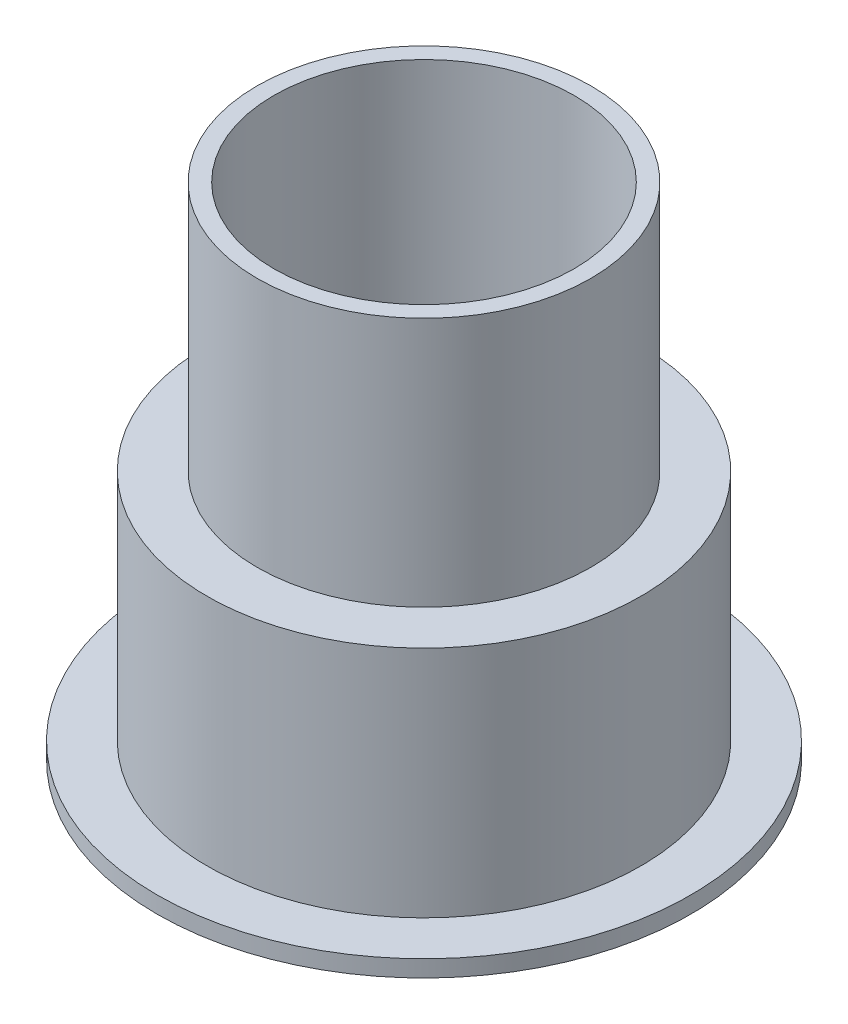
SolidWorks part; units mm, degrees
ref_plane "Front Plane" through (0, 0, 0) normal (0, 0, 1) x (1, 0, 0)
ref_plane "Top Plane" through (0, 0, 0) normal (0, 1, 0) x (1, 0, 0)
ref_plane "Right Plane" through (0, 0, 0) normal (1, 0, 0) x (0, 0, -1)
sketch "Sketch1" plane through (0, 0, 0) normal (0, 0, 1) x (1, 0, 0)
  line L0 (0, 0) -> (0, 13.5207) construction
  line L1 (6, -0.8548) -> (6, 6.1452)
  line L2 (6, 6.1452) -> (0, 6.1452)
  line L3 (4.5, 6.6452) -> (4.5, 14.1452)
  line L4 (6, -0.8548) -> (8, -0.8548)
  line L5 (5, 6.6452) -> (5, 14.1452)
  line L6 (6.5, -0.3548) -> (8, -0.3548)
  line L7 (6.5, -0.3548) -> (6.5, 6.6452)
  line L8 (6.5, 6.6452) -> (5, 6.6452)
  line L9 (0, 6.6452) -> (0, 6.1452)
  line L10 (4.5, 14.1452) -> (5, 14.1452)
  line L11 (8, -0.8548) -> (8, -0.3548)
  line L12 (4.5, 6.1452) -> (4.5, 14.1452) construction
  line L13 (4.5, 6.6452) -> (0, 6.6452)
  line L14 (6.5, 6.6452) -> (0, 6.6452) construction
  line L15 (5, 6.1452) -> (5, 14.1452) construction
  dimension "D1" = 6
  dimension "D2" = 2
  dimension "D3" = 7
  dimension "D5" = 1.5
  dimension "D6" = 0.5
  dimension "D7" = 0.5
revolve "Revolve1" add sketch "Sketch1" angle 360 about L0
